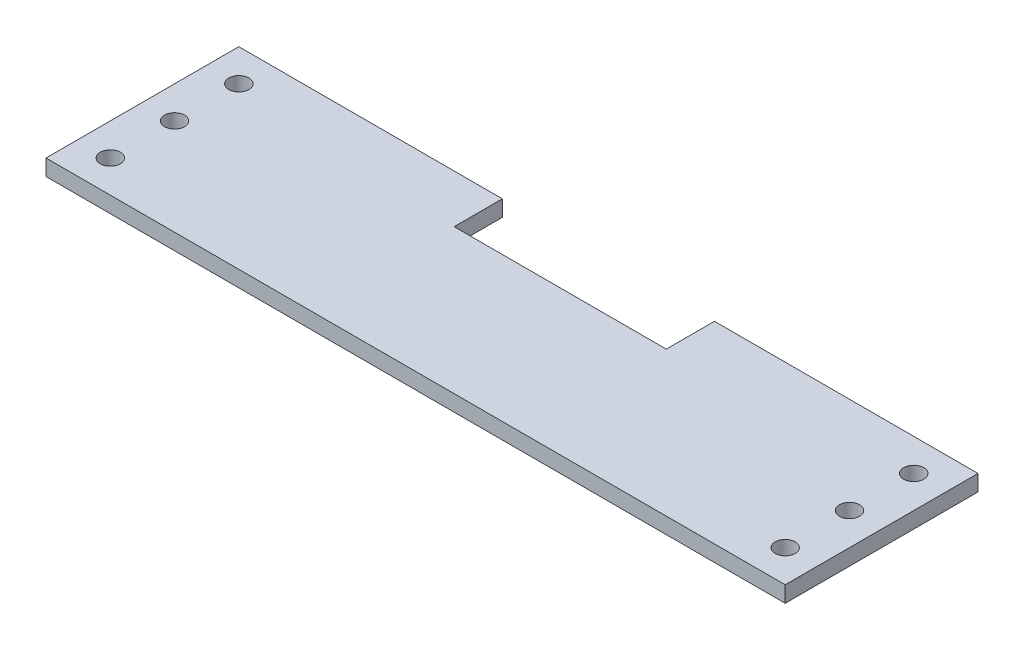
SolidWorks part; units mm, degrees
ref_plane "Front Plane" through (0, 0, 0) normal (0, 0, 1) x (1, 0, 0)
ref_plane "Top Plane" through (0, 0, 0) normal (0, 1, 0) x (1, 0, 0)
ref_plane "Right Plane" through (0, 0, 0) normal (1, 0, 0) x (0, 0, -1)
sketch "Sketch1" plane through (0, 0, 0) normal (0, 1, 0) x (1, 0, 0)
  line L0 (12.7, 76.2) -> (12.7, 0) construction
  line L1 (0, 0) -> (292.1, 0)
  line L2 (0, 0) -> (0, 76.2)
  line L3 (0, 76.2) -> (292.1, 76.2)
  line L4 (292.1, 0) -> (292.1, 76.2)
  line L5 (146.05, 76.2) -> (146.05, 0) construction
  line L6 (279.4, 76.2) -> (279.4, 0) construction
  circle A0 centre (12.7, 63.5) radius 3.9688
  circle A1 centre (12.7, 38.1) radius 3.9688
  circle A2 centre (12.7, 12.7) radius 3.9688
  circle A3 centre (279.4, 12.7) radius 3.9688
  circle A4 centre (279.4, 38.1) radius 3.9687
  circle A5 centre (279.4, 63.5) radius 3.9687
  dimension "D8" = 7.9375
  dimension "D9" = 7.9375
  dimension "D10" = 7.9375
  dimension "D1" = 76.2
  dimension "D2" = 292.1
  dimension "D3" = 12.7
  dimension "D5" = 12.7
  dimension "D6" = 25.4
  dimension "D7" = 25.4
extrude "Boss-Extrude1" add sketch "Sketch1" along normal blind 6.35
sketch "Sketch2" plane through (0, 6.35, 0) normal (0, 1, 0) x (1, 0, 0)
  line L0 (0, 76.2) -> (0, 0) construction
  line L1 (0, 0) -> (292.1, 0) construction
  line L2 (292.1, 0) -> (292.1, 76.2) construction
  line L3 (292.1, 76.2) -> (0, 76.2) construction
  line L5 (104.14, 76.2) -> (187.96, 76.2)
  line L6 (104.14, 76.2) -> (104.14, 57.15)
  line L7 (104.14, 57.15) -> (187.96, 57.15)
  line L8 (187.96, 76.2) -> (187.96, 57.15)
  point P12 (146.05, 76.2)
  dimension "D1" = 104.14
  dimension "D2" = 19.05
extrude "Master Cylinder Opening" cut sketch "Sketch2" against normal up to next
